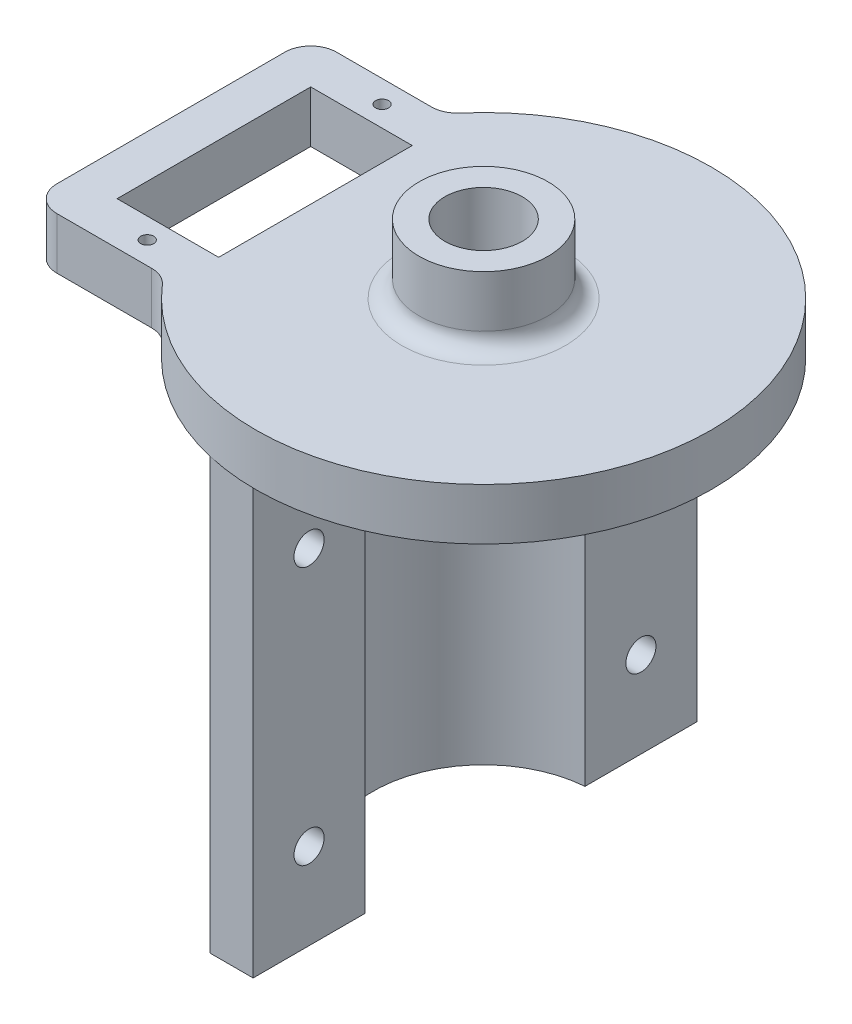
SolidWorks part; units mm, degrees
ref_plane "Front Plane" through (0, 0, 0) normal (0, 0, 1) x (1, 0, 0)
ref_plane "Top Plane" through (0, 0, 0) normal (0, 1, 0) x (1, 0, 0)
ref_plane "Right Plane" through (0, 0, 0) normal (1, 0, 0) x (0, 0, -1)
sketch "Sketch6" plane through (0, 0, 0) normal (0, -1, 0) x (1, 0, 0)
  line L5 (-1, 25.7848) -> (-1, 12.786)
  line L6 (-1, 25.7848) -> (-6, 25.7848)
  line L7 (-6, 25.7848) -> (-6, 16.7848)
  line L8 (-6, -16.7848) -> (-6, -25.7848)
  line L9 (-6, -25.7848) -> (-1, -25.7848)
  line L10 (-1, -25.7848) -> (-1, -12.786)
  line L11 (-12.825, 0) -> (-17.825, 0) construction
  arc A0 (-1, 12.786) -> (-1, -12.786) centre (0, 0) ccw
  arc A1 (-6, 16.7848) -> (-6, -16.7848) centre (0, 0) ccw
  dimension "D1" = 25.65
  dimension "D2" = 5
  dimension "D3" = 1
  dimension "D4" = 9
extrude "Boss-Extrude4" add sketch "Sketch6" along normal blind 50
sketch "Sketch7" plane through (-1, 0, 0) normal (1, 0, 0) x (0, 0, -1)
  line L0 (-19.2854, -50) -> (-19.2854, 0) construction
  line L3 (0, 0) -> (0, -50) construction
  line L6 (-25.7848, -25) -> (25.7848, -25) construction
  line L11 (-12.786, 0) -> (-25.7848, 0) construction
  line L12 (-12.786, -50) -> (-25.7848, -50) construction
  line L13 (-25.7848, -50) -> (-25.7848, 0) construction
  line L14 (25.7848, -50) -> (25.7848, 0) construction
  line L15 (-12.786, -50) -> (12.786, -50) construction
  circle A0 centre (-19.2854, -10) radius 1.75
  circle A1 centre (-19.2854, -40) radius 1.75
  circle A2 centre (19.2854, -40) radius 1.75
  circle A3 centre (19.2854, -10) radius 1.75
  dimension "D1" = 10
  dimension "D2" = 3.5
extrude "Cut-Extrude1" cut sketch "Sketch7" against normal through all
sketch "Sketch8" plane through (0, 0, 0) normal (0, 1, 0) x (1, 0, 0)
  line L0 (-25.4436, -13.65) -> (-25.4436, 13.65) construction
  line L1 (-31.3436, -11.25) -> (-19.5436, -11.25)
  line L2 (-31.3436, -11.25) -> (-31.3436, 11.25)
  line L3 (-31.3436, 11.25) -> (-19.5436, 11.25)
  line L4 (-19.5436, -11.25) -> (-19.5436, 11.25)
  line L5 (-33.3436, -16.25) -> (-22.319, -16.25)
  line L6 (-36.3436, -13.25) -> (-36.3436, 13.25)
  line L7 (-33.3436, 16.25) -> (-22.319, 16.25)
  circle A1 centre (-25.4436, 13.65) radius 0.75
  circle A2 centre (-25.4436, -13.65) radius 0.75
  arc A3 (-20.0472, -17.2906) -> (-20.0472, 17.2906) centre (0, 0) ccw
  arc A4 (-33.3436, -16.25) -> (-36.3436, -13.25) centre (-33.3436, -13.25) cw
  arc A5 (-36.3436, 13.25) -> (-33.3436, 16.25) centre (-33.3436, 13.25) cw
  arc A6 (-22.319, 16.25) -> (-20.0472, 17.2906) centre (-22.319, 19.25) ccw
  arc A7 (-22.319, -16.25) -> (-20.0472, -17.2906) centre (-22.319, -19.25) cw
  circle A8 centre (-25.4436, 5.35) radius 5.9 construction
  point P7 (-19.5436, 0)
  point P13 (-25.4436, -11.25)
  point P18 (-25.4436, 0)
  point P24 (-36.3436, 0)
  dimension "D1" = 5
  dimension "D4" = 1.5
  dimension "D7" = 5
  dimension "D8" = 3
  dimension "D9" = 3
  dimension "D10" = 11.8
  dimension "D2" = 11.8
  dimension "D3" = 22.5
  dimension "D5" = 27.3
  dimension "D6" = 26
extrude "Boss-Extrude5" add sketch "Sketch8" along normal blind 6
sketch "Sketch9" plane through (0, 6, 0) normal (0, 1, 0) x (1, 0, 0)
  circle A0 centre (0, 0) radius 7.5
  dimension "D1" = 15
extrude "Boss-Extrude6" add sketch "Sketch9" along normal blind 8
fillet "Fillet1" radius 2 1 edges at (0, 6, 7.5)
sketch "Sketch10" plane through (0, 14, 0) normal (0, 1, 0) x (1, 0, 0)
  circle A0 centre (0, 0) radius 4.5
  dimension "D1" = 9
extrude "Cut-Extrude2" cut sketch "Sketch10" against normal through all
